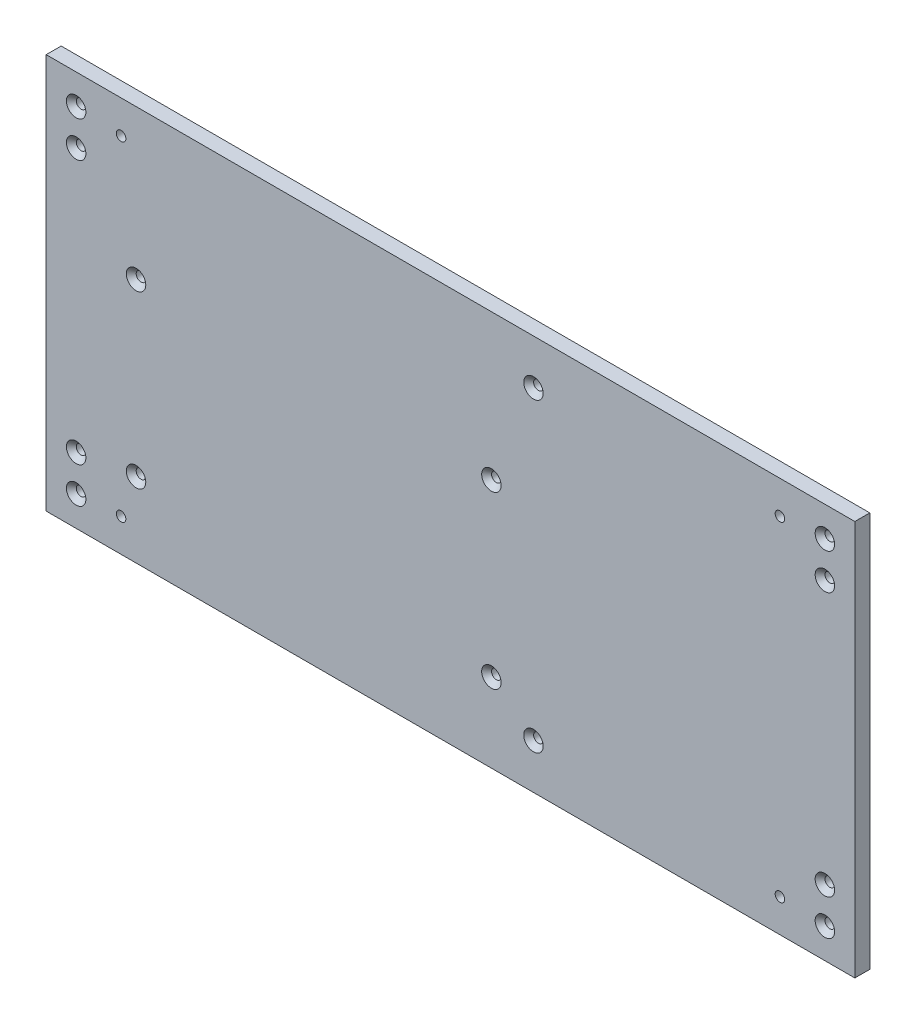
SolidWorks part; units mm, degrees
material "Polycarbonate (PC)"
ref_plane "Front Plane" through (0, 0, 0) normal (0, 0, 1) x (1, 0, 0)
ref_plane "Top Plane" through (0, 0, 0) normal (0, 1, 0) x (1, 0, 0)
ref_plane "Right Plane" through (0, 0, 0) normal (1, 0, 0) x (0, 0, -1)
sketch "Sketch1" plane through (0, 0, 0) normal (0, 0, 1) x (1, 0, 0)
  line L1 (135, -66) -> (-135, -66)
  line L2 (135, -66) -> (135, 66)
  line L3 (135, 66) -> (-135, 66)
  line L4 (-135, -66) -> (-135, 66)
  line L5 (135, -66) -> (-135, 66) construction
  line L6 (135, 66) -> (-135, -66) construction
  point P0 (0, 0)
  dimension "D1" = 270
  dimension "D2" = 132
extrude "Sheet" add sketch "Sketch1" along normal mid plane 5
hole_wizard "Ø3.2 (3.2) WallMountHoles" positions "Sketch6" profile "Sketch7" hole size "Ø3.2" standard "ANSI Metric" end condition through all
sketch "Sketch6" plane through (0, 0, 2.5) normal (0, 0, 1) x (1, 0, 0)
  line L0 (135, 66) -> (-135, 66) construction
  line L1 (-135, -66) -> (-135, 66) construction
  line L4 (135, -66) -> (135, 66) construction
  line L5 (135, -66) -> (-135, -66) construction
  point P0 (-125, 56)
  point P2 (-125, 44)
  point P4 (-125, -44)
  point P6 (-125, -56)
  point P8 (125, -56)
  point P10 (125, -44)
  point P12 (125, 44)
  point P14 (125, 56)
  point P45 (27.7, -51)
  point P47 (27.7, 51)
  dimension "D1" = 10
  dimension "D2" = 22
  dimension "D4" = 10
  dimension "D3" = 10
  dimension "D5" = 10
  dimension "D6" = 22
  dimension "D7" = 15
  dimension "D8" = 15
  dimension "D9" = 162.7
sketch "Sketch7" plane through (-125, 56, 2.5) normal (1, 0, 0) x (0, -1, 0)
  line L0 (0, 0) -> (0, 5)
  line L1 (0, 5) -> (1.6, 5)
  line L2 (1.6, 5) -> (1.6, 1.65)
  line L3 (1.6, 1.65) -> (3.25, 0)
  line L5 (3.25, 0) -> (0, 0)
  line L6 (-1.6, 1.65) -> (-3.25, 0) construction
  line L11 (0, -6.35) -> (0, 107.95) construction
  dimension "Thru Hole Dia." = 3.2
  dimension "Thru Hole Depth" = 5
  dimension "Near C'Sink Dia." = 6.5
  dimension "Near C'Sink Angle" = 90
hole_wizard "Ø3.2 (3.2) FeetMountHoles" positions "Sketch9" profile "Sketch8" hole size "Ø3.2" standard "ANSI Metric" end condition through all
sketch "Sketch9" plane through (0, 0, 2.5) normal (0, 0, 1) x (1, 0, 0)
  line L0 (135, -66) -> (-135, -66) construction
  line L1 (135, -66) -> (135, 66) construction
  point P0 (110, 55)
  point P2 (-110, 55)
  point P4 (-110, -55)
  point P6 (110, -55)
  dimension "D1" = 220
  dimension "D2" = 110
  dimension "D3" = 11
  dimension "D4" = 25
sketch "Sketch8" plane through (110, 55, 2.5) normal (1, 0, 0) x (0, -1, 0)
  line L0 (0, 0) -> (0, 5)
  line L1 (0, 5) -> (1.6, 5)
  line L2 (1.6, 5) -> (1.6, 0)
  line L5 (1.6, 0) -> (0, 0)
  line L11 (0, -6.35) -> (0, 107.95) construction
  dimension "Thru Hole Dia." = 3.2
  dimension "Thru Hole Depth" = 5
hole_wizard "Ø3.2 (3.2) PSUHoles" positions "Sketch10" profile "Sketch11" hole size "Ø3.2" standard "ANSI Metric" end condition through all
sketch "Sketch10" plane through (0, 0, 2.5) normal (0, 0, 1) x (1, 0, 0)
  line L2 (-135, -66) -> (-135, 66) construction
  line L3 (135, -66) -> (-135, -66) construction
  line L4 (135, 66) -> (-135, 66) construction
  point P0 (13.65, -39.65)
  point P2 (-105, 16)
  point P11 (13.65, 17.35)
  point P13 (-105, -41)
  dimension "D1" = 1.35
  dimension "D2" = 1.35
  dimension "D3" = 25
  dimension "D4" = 30
  dimension "D5" = 118.65
  dimension "D6" = 50
sketch "Sketch11" plane through (13.65, -39.65, 2.5) normal (1, 0, 0) x (0, -1, 0)
  line L0 (0, 0) -> (0, 5)
  line L1 (0, 5) -> (1.6, 5)
  line L2 (1.6, 5) -> (1.6, 1.65)
  line L3 (1.6, 1.65) -> (3.25, 0)
  line L5 (3.25, 0) -> (0, 0)
  line L6 (-1.6, 1.65) -> (-3.25, 0) construction
  line L11 (0, -6.35) -> (0, 107.95) construction
  dimension "Thru Hole Dia." = 3.2
  dimension "Thru Hole Depth" = 5
  dimension "Near C'Sink Dia." = 6.5
  dimension "Near C'Sink Angle" = 90
equation "\"D3@Sketch6\"=\"D4@Sketch6\""
equation "\"D5@Sketch6\"=\"D1@Sketch6\""
equation "\"D6@Sketch6\"=\"D2@Sketch6\""
equation "\"D3@Sketch9\"=(\"D2@Sketch1\"-\"D2@Sketch9\")/2"
equation "\"D4@Sketch9\"=(\"D1@Sketch1\"-\"D1@Sketch9\")/2"
equation "\"D7@Sketch6\"=\"D8@Sketch6\""
